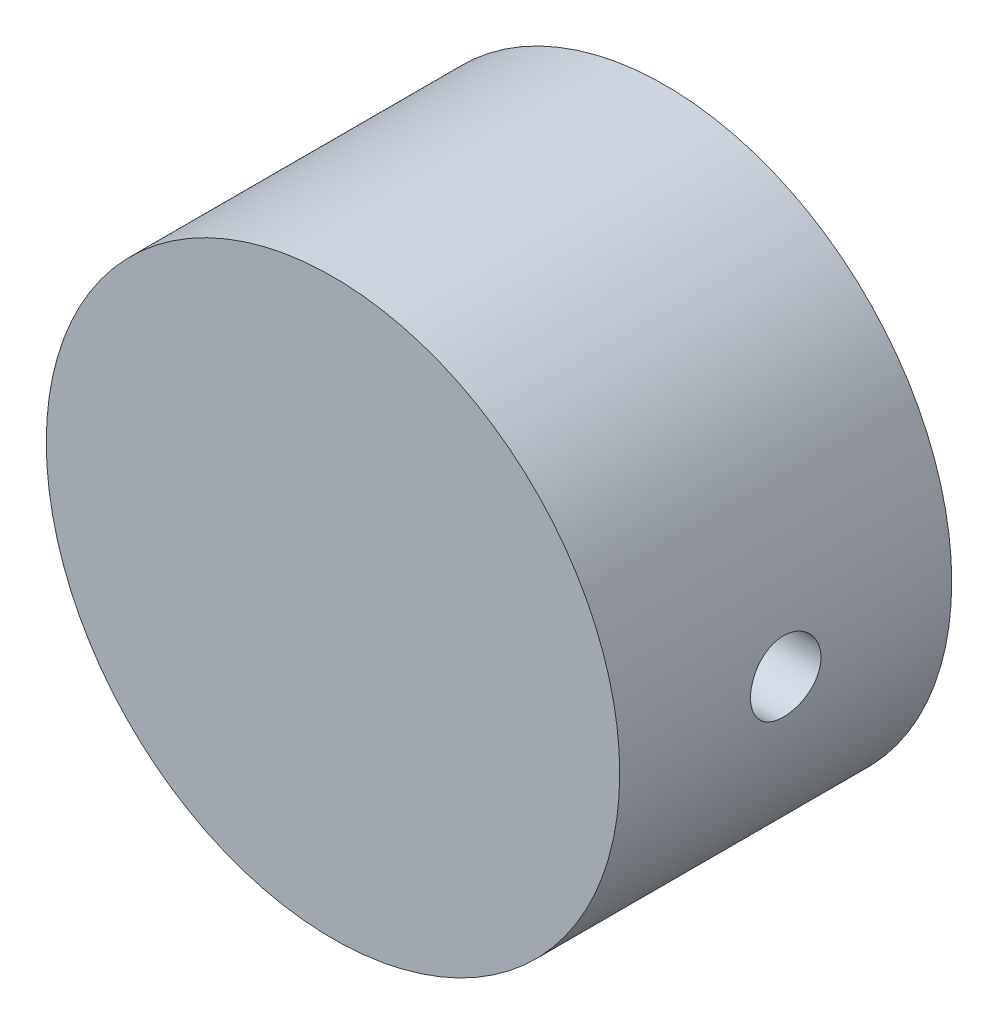
SolidWorks part; units mm, degrees
ref_plane "Plan de face" through (0, 0, 0) normal (0, 0, 1) x (1, 0, 0)
ref_plane "Plan de dessus" through (0, 0, 0) normal (0, 1, 0) x (1, 0, 0)
ref_plane "Plan de droite" through (0, 0, 0) normal (1, 0, 0) x (0, 0, -1)
sketch "Esquisse1" plane through (0, 0, 0) normal (0, 0, 1) x (1, 0, 0)
  circle A0 centre (0, 0) radius 28.5
extrude "Boss.-Extru.1" add sketch "Esquisse1" along normal blind 33
ref_plane "Plan1" through (0, 0, 43) normal (0, 0, 1) x (1, 0, 0)
sketch "Esquisse3" plane through (0, 0, 43) normal (0, 0, 1) x (1, 0, 0)
  line L0 (0, 28.5) -> (0, -28.5) construction
  circle A0 centre (0, 0) radius 28.5 construction
ref_plane "Plan2" through (0, 28.5, 43) normal (0, -1, 0) x (-1, 0, 0)
sketch "Esquisse5" plane through (0, 28.5, 43) normal (0, -1, 0) x (-1, 0, 0)
  line L0 (0, 10) -> (0, 43) construction
  line L1 (-28.5, 10) -> (28.5, 10) construction
  line L2 (-28.5, 26.5) -> (28.5, 26.5) construction
  line L3 (-28.5, 43) -> (-28.5, 10) construction
  line L4 (28.5, 10) -> (28.5, 43) construction
  circle A0 centre (0, 26.5) radius 3.5
  point P13 (0, 10)
ref_plane "Plan3" through (0, 0, 0) normal (-1, 0, 0) x (0, 0, 1)
sketch "Esquisse6" plane through (0, 0, 0) normal (-1, 0, 0) x (0, 0, 1)
  line L0 (16.5, 28.5) -> (16.5, -28.5) construction
  line L1 (13, 28.5) -> (20, 28.5) construction
  line L2 (0, -28.5) -> (33, -28.5) construction
  line L3 (0, 0) -> (33, 0) construction
  line L4 (33, -28.5) -> (33, 28.5) construction
  circle A0 centre (16.5, 0) radius 3.5
extrude "Enlèv. mat.-Extru.2" cut sketch "Esquisse6" against normal through all both and the other way through all
